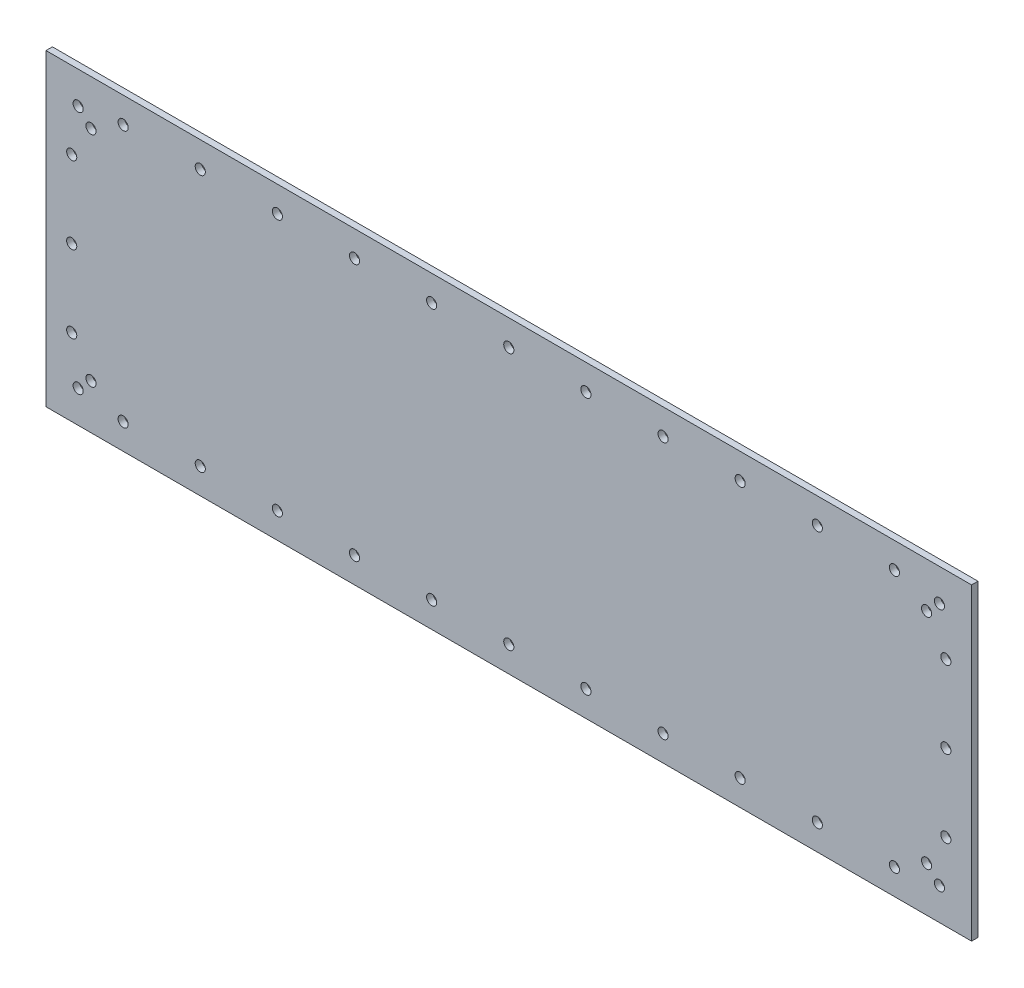
SolidWorks part; units mm, degrees
ref_plane "Front Plane" through (0, 0, 0) normal (0, 0, 1) x (1, 0, 0)
ref_plane "Top Plane" through (0, 0, 0) normal (0, 1, 0) x (1, 0, 0)
ref_plane "Right Plane" through (0, 0, 0) normal (1, 0, 0) x (0, 0, -1)
sketch "Sketch1" plane through (0, 0, 0) normal (0, 0, 1) x (1, 0, 0)
  line L0 (0, 0) -> (-228.6, 0) construction
  line L1 (228.6, -76.2) -> (-228.6, -76.2)
  line L2 (228.6, -76.2) -> (228.6, 76.2)
  line L3 (228.6, 76.2) -> (-228.6, 76.2)
  line L4 (-228.6, -76.2) -> (-228.6, 76.2)
  line L5 (228.6, -76.2) -> (-228.6, 76.2) construction
  line L6 (228.6, 76.2) -> (-228.6, -76.2) construction
  line L7 (0, 0) -> (0, 76.2) construction
  line L8 (-215.9, 38.1) -> (-215.9, 0) construction
  line L9 (215.9, 38.1) -> (215.9, 0) construction
  circle A0 centre (212.725, 60.325) radius 2.5
  circle A1 centre (206.375, 53.975) radius 2.5
  circle A2 centre (-206.375, 53.975) radius 2.5
  circle A3 centre (-212.725, 60.325) radius 2.5
  circle A4 centre (-212.725, -60.325) radius 2.5
  circle A5 centre (-206.375, -53.975) radius 2.5
  circle A6 centre (206.375, -53.975) radius 2.5
  circle A7 centre (212.725, -60.325) radius 2.5
  circle A8 centre (-190.5, 63.5) radius 2.5
  circle A9 centre (-152.4, 63.5) radius 2.5
  circle A10 centre (-114.3, 63.5) radius 2.5
  circle A11 centre (-76.2, 63.5) radius 2.5
  circle A12 centre (-38.1, 63.5) radius 2.5
  circle A13 centre (0, 63.5) radius 2.5
  circle A14 centre (38.1, 63.5) radius 2.5
  circle A15 centre (76.2, 63.5) radius 2.5
  circle A16 centre (114.3, 63.5) radius 2.5
  circle A17 centre (152.4, 63.5) radius 2.5
  circle A18 centre (190.5, 63.5) radius 2.5
  circle A19 centre (-215.9, 38.1) radius 2.5
  circle A20 centre (-215.9, 0) radius 2.5
  circle A21 centre (-215.9, -38.1) radius 2.5
  circle A22 centre (190.5, -63.5) radius 2.5
  circle A23 centre (152.4, -63.5) radius 2.5
  circle A24 centre (114.3, -63.5) radius 2.5
  circle A25 centre (76.2, -63.5) radius 2.5
  circle A26 centre (38.1, -63.5) radius 2.5
  circle A27 centre (0, -63.5) radius 2.5
  circle A28 centre (-38.1, -63.5) radius 2.5
  circle A29 centre (-76.2, -63.5) radius 2.5
  circle A30 centre (-114.3, -63.5) radius 2.5
  circle A31 centre (-152.4, -63.5) radius 2.5
  circle A32 centre (-190.5, -63.5) radius 2.5
  circle A33 centre (215.9, -38.1) radius 2.5
  circle A34 centre (215.9, 0) radius 2.5
  circle A35 centre (215.9, 38.1) radius 2.5
  point P0 (0, 0)
  dimension "D5" = 5
  dimension "D1" = 152.4
  dimension "D2" = 457.2
  dimension "D3" = 15.875
  dimension "D4" = 15.875
  dimension "D6" = 22.225
  dimension "D7" = 22.225
  dimension "D8" = 38.1
  dimension "D9" = 12.7
  dimension "D11" = 38.1
  dimension "D12" = 38.1
  dimension "D13" = 12.7
  dimension "D15" = 38.1
  dimension "D10" = 11
  dimension "D14" = 3
extrude "Boss-Extrude1" add sketch "Sketch1" along normal blind 3.175
